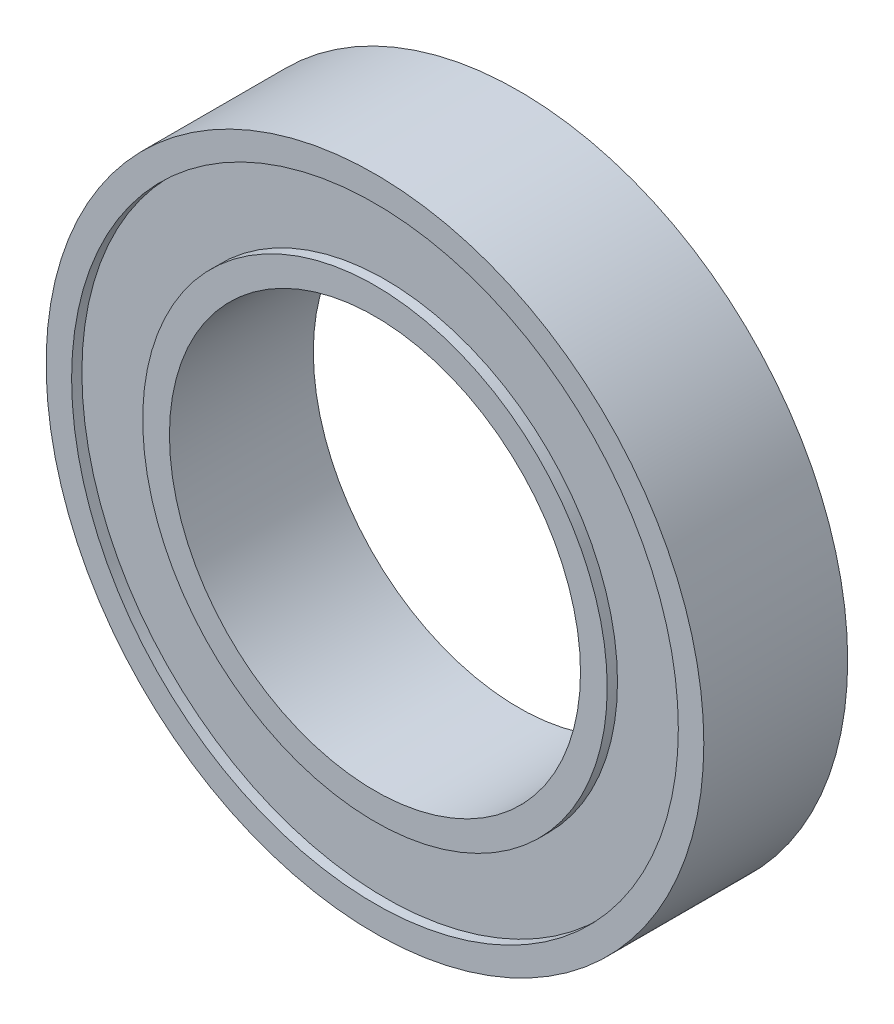
SolidWorks part; units mm, degrees
material "鑄不鏽鋼"
ref_plane "前基準面" through (0, 0, 0) normal (0, 0, 1) x (1, 0, 0)
ref_plane "上基準面" through (0, 0, 0) normal (0, 1, 0) x (1, 0, 0)
ref_plane "右基準面" through (0, 0, 0) normal (1, 0, 0) x (0, 0, -1)
sketch "草圖1" plane through (0, 0, 0) normal (0, 0, 1) x (1, 0, 0)
  circle A0 centre (0, 0) radius 16
  dimension "D1" = 32
extrude "填料-伸長1" add sketch "草圖1" along normal blind 7
sketch "草圖2" plane through (0, 0, 7) normal (0, 0, 1) x (1, 0, 0)
  circle A0 centre (0, 0) radius 10
  dimension "D1" = 20
extrude "除料-伸長1" cut sketch "草圖2" against normal through all
sketch "草圖3" plane through (0, 0, 7) normal (0, 0, 1) x (1, 0, 0)
  circle A0 centre (0, 0) radius 11.3
  circle A1 centre (0, 0) radius 14.76
  dimension "D1" = 22.6
  dimension "D2" = 29.52
extrude "除料-伸長2" cut sketch "草圖3" against normal blind 0.5
sketch "草圖4" plane through (0, 0, 0) normal (0, 0, -1) x (-1, 0, 0)
  circle A0 centre (0, 0) radius 11.3
  circle A1 centre (0, 0) radius 14.76
  dimension "D1" = 22.6
  dimension "D2" = 29.52
extrude "除料-伸長3" cut sketch "草圖4" against normal blind 0.5
